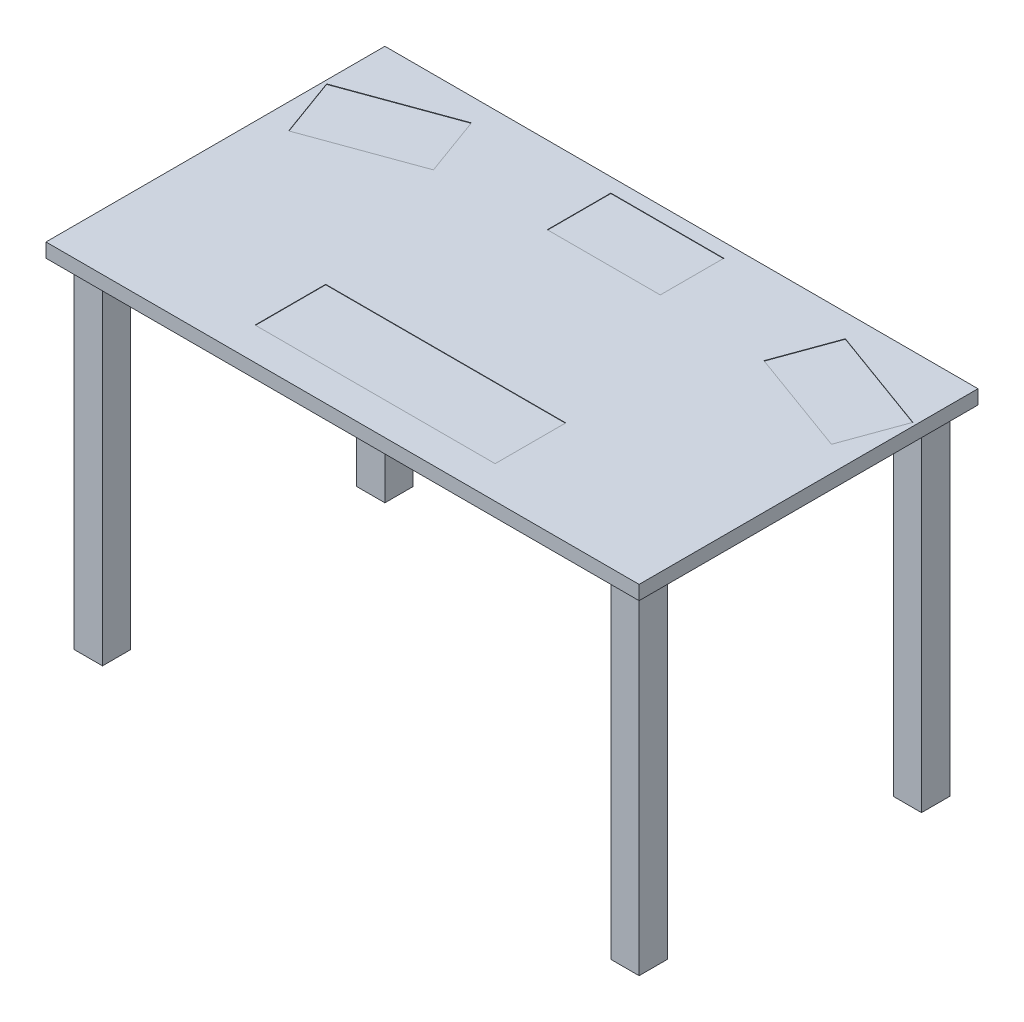
SolidWorks part; units mm, degrees
ref_plane "Front Plane" through (0, 0, 0) normal (0, 0, 1) x (1, 0, 0)
ref_plane "Top Plane" through (0, 0, 0) normal (0, 1, 0) x (1, 0, 0)
ref_plane "Right Plane" through (0, 0, 0) normal (1, 0, 0) x (0, 0, -1)
sketch "Sketch1" plane through (0, 0, 0) normal (0, 1, 0) x (1, 0, 0)
  line L0 (50.8, 0) -> (965.2, 0) construction
  line L1 (0, 0) -> (50.8, 0)
  line L2 (0, 0) -> (0, 50.8)
  line L3 (0, 50.8) -> (50.8, 50.8)
  line L4 (50.8, 0) -> (50.8, 50.8)
  line L5 (0, 50.8) -> (0, 508) construction
  line L6 (50.8, 558.8) -> (965.2, 558.8) construction
  line L7 (0, 508) -> (50.8, 508)
  line L8 (0, 508) -> (0, 558.8)
  line L9 (0, 558.8) -> (50.8, 558.8)
  line L10 (50.8, 508) -> (50.8, 558.8)
  line L12 (965.2, 558.8) -> (1016, 558.8)
  line L13 (965.2, 558.8) -> (965.2, 508)
  line L14 (965.2, 508) -> (1016, 508)
  line L15 (1016, 558.8) -> (1016, 508)
  line L16 (965.2, 0) -> (1016, 0)
  line L17 (965.2, 0) -> (965.2, 50.8)
  line L18 (965.2, 50.8) -> (1016, 50.8)
  line L19 (1016, 0) -> (1016, 50.8)
  dimension "D1" = 50.8
  dimension "D2" = 50.8
  dimension "D3" = 914.4
  dimension "D4" = 457.2
  dimension "D5" = 50.8
  dimension "D6" = 50.8
  dimension "D7" = 914.4
  dimension "D8" = 50.8
  dimension "D9" = 50.8
  dimension "D10" = 50.8
extrude "Boss-Extrude1" add sketch "Sketch1" along normal blind 609.6
sketch "Sketch2" plane through (0, 609.6, 0) normal (0, 1, 0) x (1, 0, 0)
  line L0 (0, 0) -> (-25.4, 0) construction
  line L1 (0, 0) -> (0, -25.4) construction
  line L2 (1016, 584.2) -> (1016, 558.8) construction
  line L3 (-25.4, 0) -> (-25.4, -25.4) construction
  line L4 (-25.4, -25.4) -> (0, -25.4) construction
  line L5 (1016, 558.8) -> (1041.4, 558.8) construction
  line L7 (1016, 584.2) -> (1041.4, 584.2) construction
  line L8 (1041.4, 558.8) -> (1041.4, 584.2) construction
  line L9 (-25.4, -25.4) -> (1041.4, -25.4)
  line L10 (-25.4, -25.4) -> (-25.4, 584.2)
  line L11 (-25.4, 584.2) -> (1041.4, 584.2)
  line L12 (1041.4, -25.4) -> (1041.4, 584.2)
  dimension "D1" = 25.4
  dimension "D2" = 25.4
  dimension "D3" = 25.4
  dimension "D4" = 25.4
extrude "Boss-Extrude2" add sketch "Sketch2" along normal blind 25.4
sketch "Sketch3" plane through (0, 635, 0) normal (0, 1, 0) x (1, 0, 0)
  line L0 (508, -25.4) -> (508, 33.1841)
  line L1 (-25.4, -25.4) -> (1041.4, -25.4) construction
  line L2 (723.9, 33.1841) -> (292.1, 33.1841)
  line L3 (508, 584.2) -> (508, 558.8)
  line L4 (292.1, 33.1841) -> (723.9, 33.1841)
  line L5 (292.1, 33.1841) -> (292.1, 160.1841)
  line L6 (292.1, 160.1841) -> (723.9, 160.1841)
  line L7 (723.9, 33.1841) -> (723.9, 160.1841)
  line L8 (1041.4, 584.2) -> (-25.4, 584.2) construction
  line L9 (406.4, 558.8) -> (609.6, 558.8)
  line L10 (171.6728, 542.7492) -> (-19.2728, 473.2508)
  line L11 (406.4, 558.8) -> (609.6, 558.8)
  line L12 (406.4, 558.8) -> (406.4, 444.5)
  line L13 (406.4, 444.5) -> (609.6, 444.5)
  line L14 (609.6, 558.8) -> (609.6, 444.5)
  line L15 (-25.4, 584.2) -> (76.2, 584.2) construction
  line L16 (-25.4, 584.2) -> (-25.4, 508) construction
  line L17 (-25.4, 508) -> (76.2, 508) construction
  line L18 (76.2, 584.2) -> (76.2, 508) construction
  line L19 (-19.2728, 473.2508) -> (19.8201, 365.8439)
  line L20 (171.6728, 542.7492) -> (-19.2728, 473.2508)
  line L21 (171.6728, 542.7492) -> (210.7657, 435.3424)
  line L22 (-19.2728, 473.2508) -> (19.8201, 365.8439)
  line L23 (210.7657, 435.3424) -> (19.8201, 365.8439)
  line L24 (508, 584.2) -> (508, -25.4) construction
  line L25 (939.8, 584.2) -> (939.8, 508) construction
  line L26 (1041.4, 508) -> (939.8, 508) construction
  line L27 (805.2343, 435.3424) -> (996.1799, 365.8439)
  line L28 (1035.2728, 473.2508) -> (996.1799, 365.8439)
  line L29 (844.3272, 542.7492) -> (805.2343, 435.3424)
  line L30 (844.3272, 542.7492) -> (1035.2728, 473.2508)
  line L31 (1035.2728, 473.2508) -> (996.1799, 365.8439)
  line L32 (844.3272, 542.7492) -> (1035.2728, 473.2508)
  point P7 (508, 33.1841)
  point P16 (508, 558.8)
  point P26 (76.2, 508)
  point P27 (76.2, 508)
  point P28 (76.2, 508)
  dimension "D1" = 431.8
  dimension "D2" = 127
  dimension "D3" = 25.4
  dimension "D4" = 203.2
  dimension "D5" = 114.3
  dimension "D6" = 101.6
  dimension "D7" = 76.2
  dimension "D8" = 70
  dimension "D9" = 203.2
  dimension "D11" = 114.3
extrude "Cut-Extrude1" cut sketch "Sketch3" against normal blind 0.7937 contours L23 L21 L10 L19 | L14 L9 L12 L13 | L30 L29 L27 L28 | L2 L7 L6 L5
